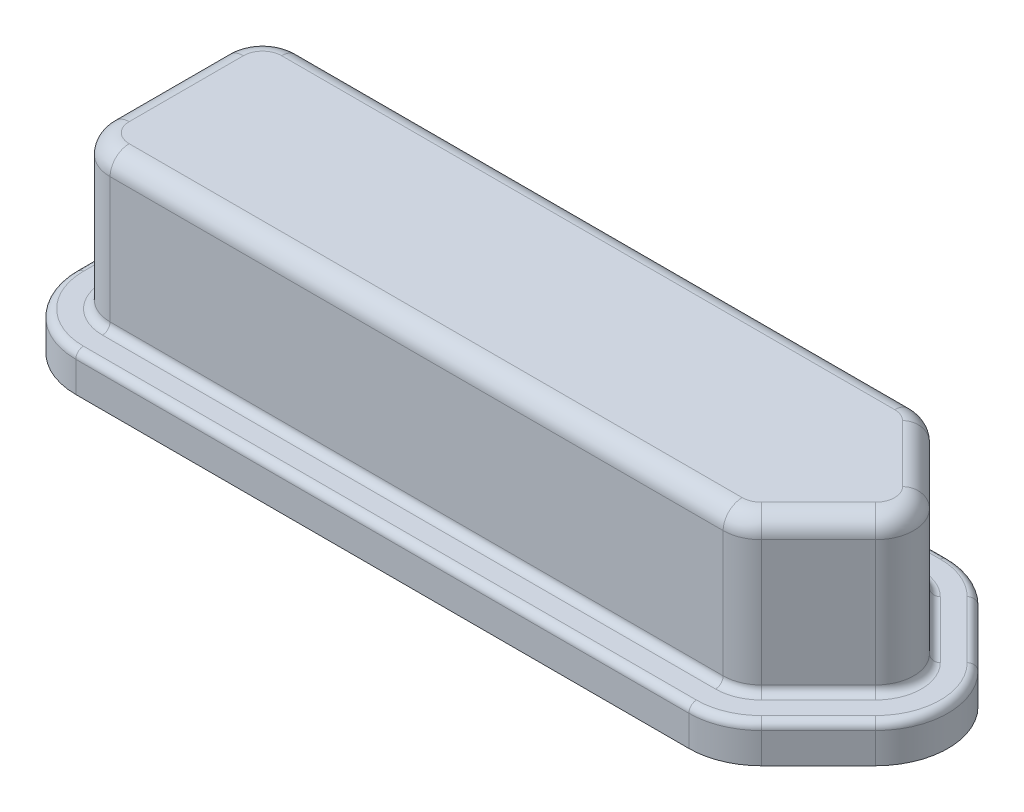
SolidWorks part; units mm, degrees
material "ABS"
ref_plane "Front Plane" through (0, 0, 0) normal (0, 0, 1) x (1, 0, 0)
ref_plane "Top Plane" through (0, 0, 0) normal (0, 1, 0) x (1, 0, 0)
ref_plane "Right Plane" through (0, 0, 0) normal (1, 0, 0) x (0, 0, -1)
sketch "Sketch1" plane through (0, 0, 0) normal (0, 1, 0) x (1, 0, 0)
  line L0 (17.5, 5) -> (20, 2.5)
  line L1 (0, 0) -> (17.5, 0)
  line L2 (0, 0) -> (0, 5)
  line L3 (0, 5) -> (17.5, 5)
  line L5 (20, 2.5) -> (17.5, 0)
  line L6 (0, 2.5) -> (20, 2.5) construction
  dimension "D1" = 20
  dimension "D2" = 5
  dimension "D3" = 135
extrude "Boss-Extrude1" add sketch "Sketch1" along normal blind 4
fillet "Fillet1" radius 1 5 edges at (17.5, 2, -5) (0, 2, -5) (0, 2, 0) (17.5, 2, 0) (20, 2, -2.5)
fillet "Fillet2" radius 0.5 10 edges at (19.5858, 4, -2.5) (18.5429, 4, -1.0429) (17.4685, 4, -0.0761) (9.0429, 4, 0) (0.2929, 4, -0.2929) (0, 4, -2.5) (0.2929, 4, -4.7071) (9.0429, 4, -5) (17.4685, 4, -4.9239) (18.5429, 4, -3.9571)
sketch "Sketch2" plane through (0, 0, 0) normal (0, -1, 0) x (1, 0, 0)
  line L10 (1, -5.9) -> (17.0858, -5.9)
  line L11 (18.4293, -5.3435) -> (19.9293, -3.8435)
  line L12 (19.9293, -1.1565) -> (18.4293, 0.3435)
  line L13 (17.0858, 0.9) -> (1, 0.9)
  line L14 (-0.9, -1) -> (-0.9, -4)
  line L15 (1, -5.9) -> (17.0858, -5.9)
  line L16 (18.4293, -5.3435) -> (19.9293, -3.8435)
  line L17 (19.9293, -1.1565) -> (18.4293, 0.3435)
  line L18 (17.0858, 0.9) -> (1, 0.9)
  line L19 (-0.9, -1) -> (-0.9, -4)
  arc A10 (17.0858, -5.9) -> (18.4293, -5.3435) centre (17.0858, -4) ccw
  arc A11 (19.9293, -3.8435) -> (19.9293, -1.1565) centre (18.5858, -2.5) ccw
  arc A12 (18.4293, 0.3435) -> (17.0858, 0.9) centre (17.0858, -1) ccw
  arc A13 (1, 0.9) -> (-0.9, -1) centre (1, -1) ccw
  arc A14 (-0.9, -4) -> (1, -5.9) centre (1, -4) ccw
  arc A15 (17.0858, -5.9) -> (18.4293, -5.3435) centre (17.0858, -4) ccw
  arc A16 (19.9293, -3.8435) -> (19.9293, -1.1565) centre (18.5858, -2.5) ccw
  arc A17 (18.4293, 0.3435) -> (17.0858, 0.9) centre (17.0858, -1) ccw
  arc A18 (1, 0.9) -> (-0.9, -1) centre (1, -1) ccw
  arc A19 (-0.9, -4) -> (1, -5.9) centre (1, -4) ccw
  dimension "D1" = 0.9
extrude "Boss-Extrude2" add sketch "Sketch2" along normal blind 1
fillet "Fillet3" radius 0.2 10 edges at (0.2929, 0, -4.7071) (9.0429, 0, -5) (17.4685, 0, -4.9239) (18.5429, 0, -3.9571) (19.5858, 0, -2.5) (18.5429, 0, -1.0429) (17.4685, 0, -0.0761) (9.0429, 0, 0) (0.2929, 0, -0.2929) (0, 0, -2.5)
fillet "Fillet4" radius 0.2 10 edges at (17.8129, 0, 0.7554) (19.1793, 0, -0.4065) (20.4858, 0, -2.5) (19.1793, 0, -4.5935) (17.8129, 0, -5.7554) (9.0429, 0, -5.9) (-0.3435, 0, -5.3435) (-0.9, 0, -2.5) (-0.3435, 0, 0.3435) (9.0429, 0, 0.9)
